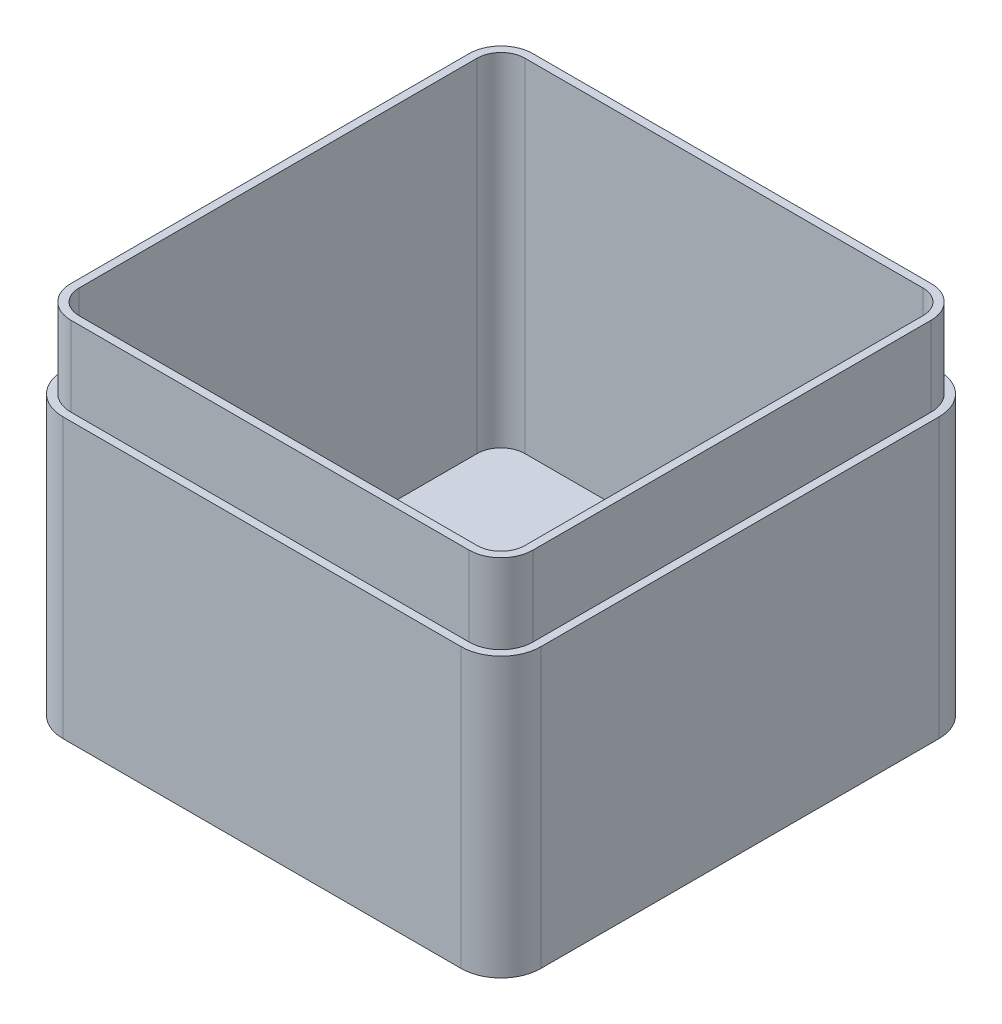
SolidWorks part; units mm, degrees
ref_plane "Front Plane" through (0, 0, 0) normal (0, 0, 1) x (1, 0, 0)
ref_plane "Top Plane" through (0, 0, 0) normal (0, 1, 0) x (1, 0, 0)
ref_plane "Right Plane" through (0, 0, 0) normal (1, 0, 0) x (0, 0, -1)
sketch "Sketch1" plane through (0, 0, 0) normal (0, 1, 0) x (1, 0, 0)
  line L1 (-60, -60) -> (60, -60)
  line L2 (-60, -60) -> (-60, 60)
  line L3 (-60, 60) -> (60, 60)
  line L4 (60, -60) -> (60, 60)
  line L5 (-60, -60) -> (60, 60) construction
  line L6 (-60, 60) -> (60, -60) construction
  point P0 (0, 0)
  dimension "D1" = 120
  dimension "D2" = 120
extrude "Boss-Extrude1" add sketch "Sketch1" along normal blind 90
fillet "Fillet1" radius 10 4 edges at (-60, 45, -60) (60, 45, -60) (60, 45, 60) (-60, 45, 60)
shell "Shell1" thickness 4
sketch "Sketch6" plane through (0, 90, 0) normal (0, 1, 0) x (1, 0, 0)
  line L0 (50, 58) -> (-50, 58)
  line L1 (-58, 50) -> (-58, -50)
  line L2 (-50, -58) -> (50, -58)
  line L3 (58, -50) -> (58, 50)
  line L4 (50, 60) -> (-50, 60)
  line L5 (-60, 50) -> (-60, -50)
  line L6 (-50, -60) -> (50, -60)
  line L7 (60, -50) -> (60, 50)
  line L8 (50, 60) -> (-50, 60)
  line L9 (-60, 50) -> (-60, -50)
  line L10 (-50, -60) -> (50, -60)
  line L11 (60, -50) -> (60, 50)
  arc A0 (-50, 58) -> (-58, 50) centre (-50, 50) ccw
  arc A1 (-58, -50) -> (-50, -58) centre (-50, -50) ccw
  arc A2 (50, -58) -> (58, -50) centre (50, -50) ccw
  arc A3 (58, 50) -> (50, 58) centre (50, 50) ccw
  arc A4 (-50, 60) -> (-60, 50) centre (-50, 50) ccw
  arc A5 (-60, -50) -> (-50, -60) centre (-50, -50) ccw
  arc A6 (50, -60) -> (60, -50) centre (50, -50) ccw
  arc A7 (60, 50) -> (50, 60) centre (50, 50) ccw
  arc A8 (-50, 60) -> (-60, 50) centre (-50, 50) ccw
  arc A9 (-60, -50) -> (-50, -60) centre (-50, -50) ccw
  arc A10 (50, -60) -> (60, -50) centre (50, -50) ccw
  arc A11 (60, 50) -> (50, 60) centre (50, 50) ccw
  dimension "D2" = 2
  dimension "D1" = 0
extrude "Cut-Extrude1" cut sketch "Sketch6" against normal blind 20
